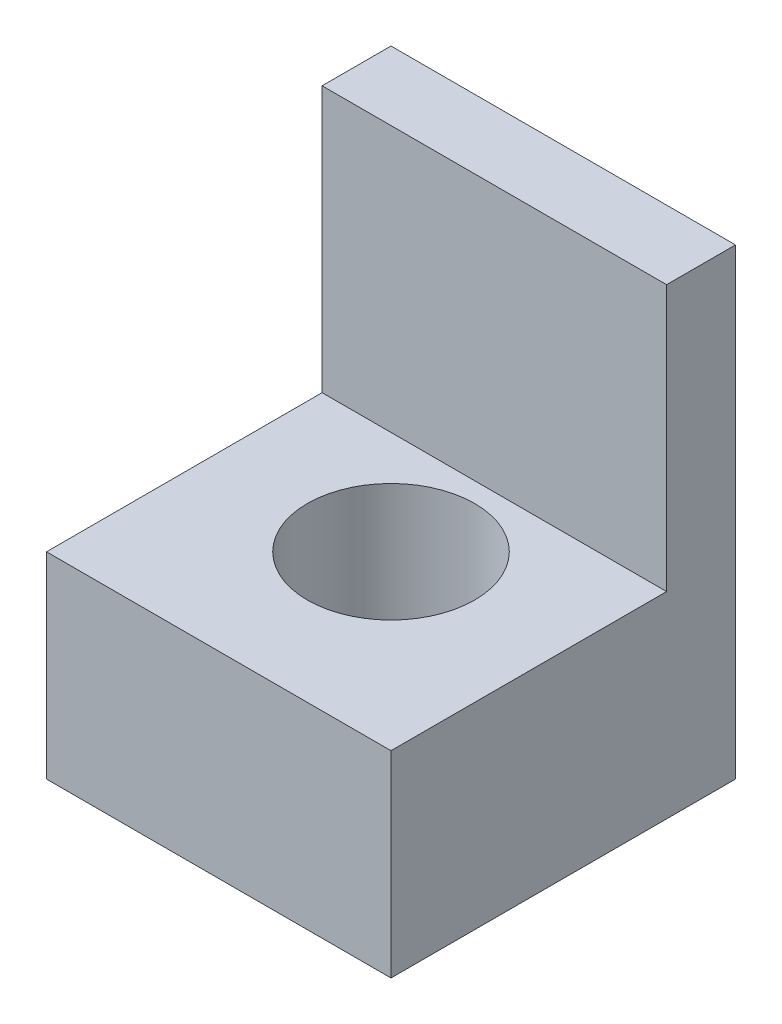
SolidWorks part; units mm, degrees
material "1060 Alloy"
ref_plane "Front Plane" through (0, 0, 0) normal (0, 0, 1) x (1, 0, 0)
ref_plane "Top Plane" through (0, 0, 0) normal (0, 1, 0) x (1, 0, 0)
ref_plane "Right Plane" through (0, 0, 0) normal (1, 0, 0) x (0, 0, -1)
sketch "Sketch1" plane through (0, 0, 0) normal (0, 1, 0) x (1, 0, 0)
  line L1 (-17.5, -17.5) -> (17.5, -17.5)
  line L2 (-17.5, -17.5) -> (-17.5, 17.5)
  line L3 (-17.5, 17.5) -> (17.5, 17.5)
  line L4 (17.5, -17.5) -> (17.5, 17.5)
  line L5 (-17.5, -17.5) -> (17.5, 17.5) construction
  line L6 (-17.5, 17.5) -> (17.5, -17.5) construction
  point P0 (0, 0)
  dimension "D1" = 35
  dimension "D2" = 35
extrude "Boss-Extrude1" add sketch "Sketch1" along normal blind 20
sketch "Sketch2" plane through (0, 20, 0) normal (0, 1, 0) x (1, 0, 0)
  line L0 (17.5, -17.5) -> (17.5, 17.5) construction
  line L1 (-17.5, 17.5) -> (17.5, 17.5)
  line L2 (-17.5, 17.5) -> (-17.5, 10.5)
  line L3 (-17.5, 10.5) -> (17.5, 10.5)
  line L4 (17.5, 17.5) -> (17.5, 10.5)
  dimension "D1" = 7
extrude "Boss-Extrude2" add sketch "Sketch2" along normal blind 27
sketch "Sketch3" plane through (0, 0, 0) normal (0, -1, 0) x (1, 0, 0)
  circle A0 centre (0, 0) radius 8.5
  dimension "D1" = 17
extrude "Cut-Extrude1" cut sketch "Sketch3" against normal blind 20
sketch "Sketch4" plane through (0, 0, 0) normal (0, 1, 0) x (1, 0, 0)
  line L0 (-17.5, -17.5) -> (17.5, -17.5) construction
  line L1 (-17.5, 10.5) -> (-17.5, -17.5) construction
  line L2 (-17.5, 10.5) -> (17.5, 10.5) construction
  circle A0 centre (-12.5, -12.5) radius 1.5
  circle A1 centre (-12.5, 5.5) radius 1.5
  circle A3 centre (12.5, -12.5) radius 1.5
  circle A4 centre (12.5, 5.5) radius 1.5
  dimension "D1" = 3
  dimension "D2" = 5
  dimension "D3" = 5
  dimension "D4" = 3
  dimension "D5" = 5
  dimension "D6" = 5
  dimension "D7" = 2
hole_wizard "M3 Tapped Hole1" positions "Sketch5" profile "Sketch7" tap size "M3" standard "ISO"
sketch "Sketch5" plane through (0, 0, 0) normal (0, -1, 0) x (-1, 0, 0)
  point P0 (-12.5, 5.5)
  point P3 (12.5, 5.5)
  point P6 (12.5, -12.5)
  point P9 (-12.5, -12.5)
sketch "Sketch7" plane through (12.5, 0, -5.5) normal (1, 0, 0) x (0, 0, -1)
  line L0 (0, 0) -> (0, 8.2511)
  line L1 (0, 8.2511) -> (1.25, 7.5)
  line L2 (1.25, 7.5) -> (1.25, 0)
  line L5 (1.25, 0) -> (0, 0)
  line L10 (0, 8.2511) -> (-1.25, 7.5) construction
  line L11 (0, -6.35) -> (0, 107.95) construction
  dimension "Tap Drill Dia." = 2.5
  dimension "Tap Drill Depth" = 7.5
  dimension "Drill Angle" = 118
cosmetic thread "Hole Thread1" parameters "D1"=6, "D2"=3
cosmetic thread "Hole Thread2" parameters "D1"=6, "D2"=3
cosmetic thread "Hole Thread3" parameters "D1"=6, "D2"=3
cosmetic thread "Hole Thread4" parameters "D1"=6, "D2"=3
